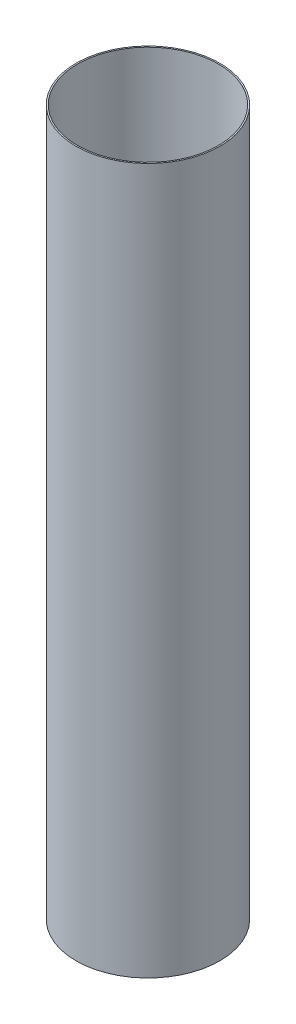
SolidWorks part; units mm, degrees
ref_plane "Alzado" through (0, 0, 0) normal (0, 0, 1) x (1, 0, 0)
ref_plane "Planta" through (0, 0, 0) normal (0, 1, 0) x (1, 0, 0)
ref_plane "Vista lateral" through (0, 0, 0) normal (1, 0, 0) x (0, 0, -1)
sketch "Croquis1" plane through (0, 0, 0) normal (0, 1, 0) x (1, 0, 0)
  circle A0 centre (0, 0) radius 150
  circle A1 centre (0, 0) radius 153
  dimension "D1" = 300
extrude "Saliente-Extruir1" add sketch "Croquis1" along normal blind 1500
